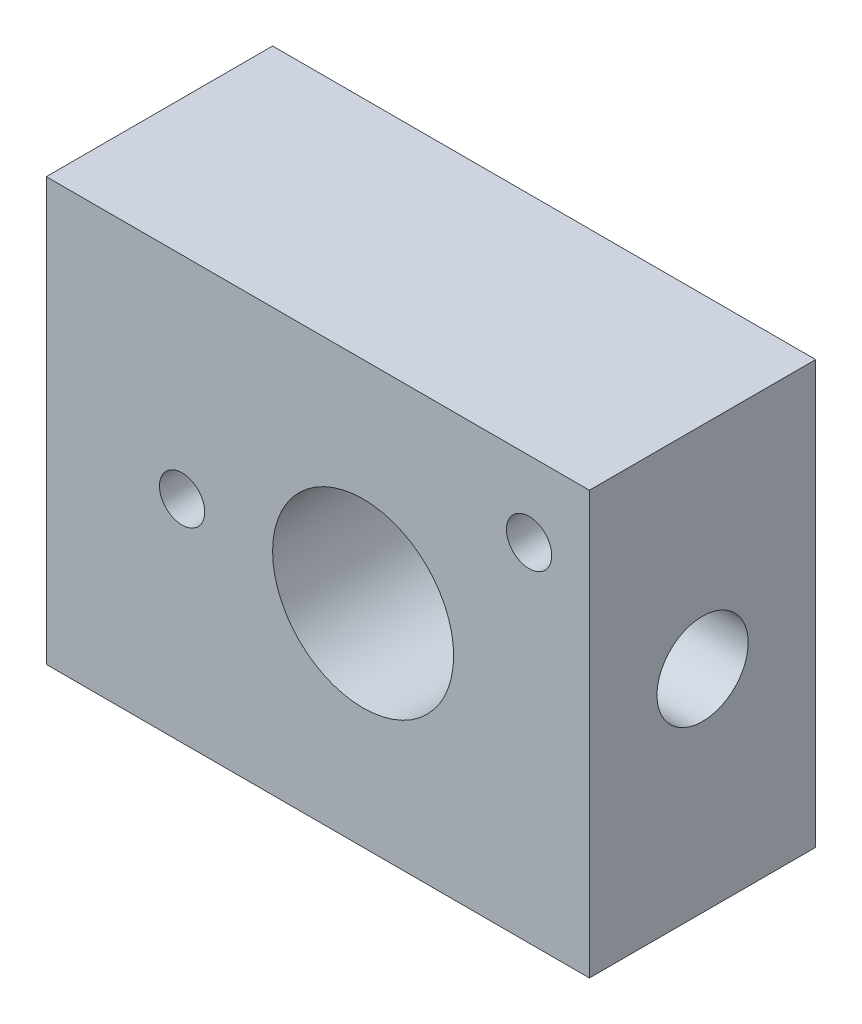
SolidWorks part; units mm, degrees
ref_plane "Ön Düzlem" through (0, 0, 0) normal (0, 0, 1) x (1, 0, 0)
ref_plane "Üst Düzlem" through (0, 0, 0) normal (0, 1, 0) x (1, 0, 0)
ref_plane "Sağ Düzlem" through (0, 0, 0) normal (1, 0, 0) x (0, 0, -1)
sketch "Çizim1" plane through (0, 0, 0) normal (0, 0, 1) x (1, 0, 0)
  line L1 (-18, -14) -> (18, -14)
  line L2 (-18, -14) -> (-18, 14)
  line L3 (-18, 14) -> (18, 14)
  line L4 (18, -14) -> (18, 14)
  line L5 (-18, -14) -> (18, 14) construction
  line L6 (-18, 14) -> (18, -14) construction
  point P0 (0, 0)
  dimension "D1" = 28
  dimension "D2" = 36
extrude "Yükseklik-Ekstrüzyon1" add sketch "Çizim1" along normal blind 15
sketch "Çizim3" plane through (0, 0, 15) normal (0, 0, 1) x (1, 0, 0)
  line L0 (-18, 14) -> (-18, -14) construction
  line L1 (18, 14) -> (-18, 14) construction
  line L2 (18, -14) -> (18, 14) construction
  circle A0 centre (3, 0) radius 6
  circle A1 centre (-9, 0) radius 1.5
  circle A2 centre (14, 9) radius 1.5
  point P13 (3, 0)
  point P14 (0, 0)
  point P16 (0, 0)
  dimension "D1" = 12
  dimension "D2" = 3
  dimension "D5" = 5
  dimension "D7" = 3
  dimension "D3" = 9
  dimension "D4" = 21
  dimension "D6" = 4
extrude "Kes-Ekstrüzyon1" cut sketch "Çizim3" against normal through all
sketch "Çizim4" plane through (18, 0, 0) normal (1, 0, 0) x (0, 0, -1)
  line L0 (-15, 14) -> (0, 14) construction
  circle A0 centre (-7.5, 0) radius 3.0221
  point P6 (-7.5, 14)
extrude "Kes-Ekstrüzyon2" cut sketch "Çizim4" against normal up to next
